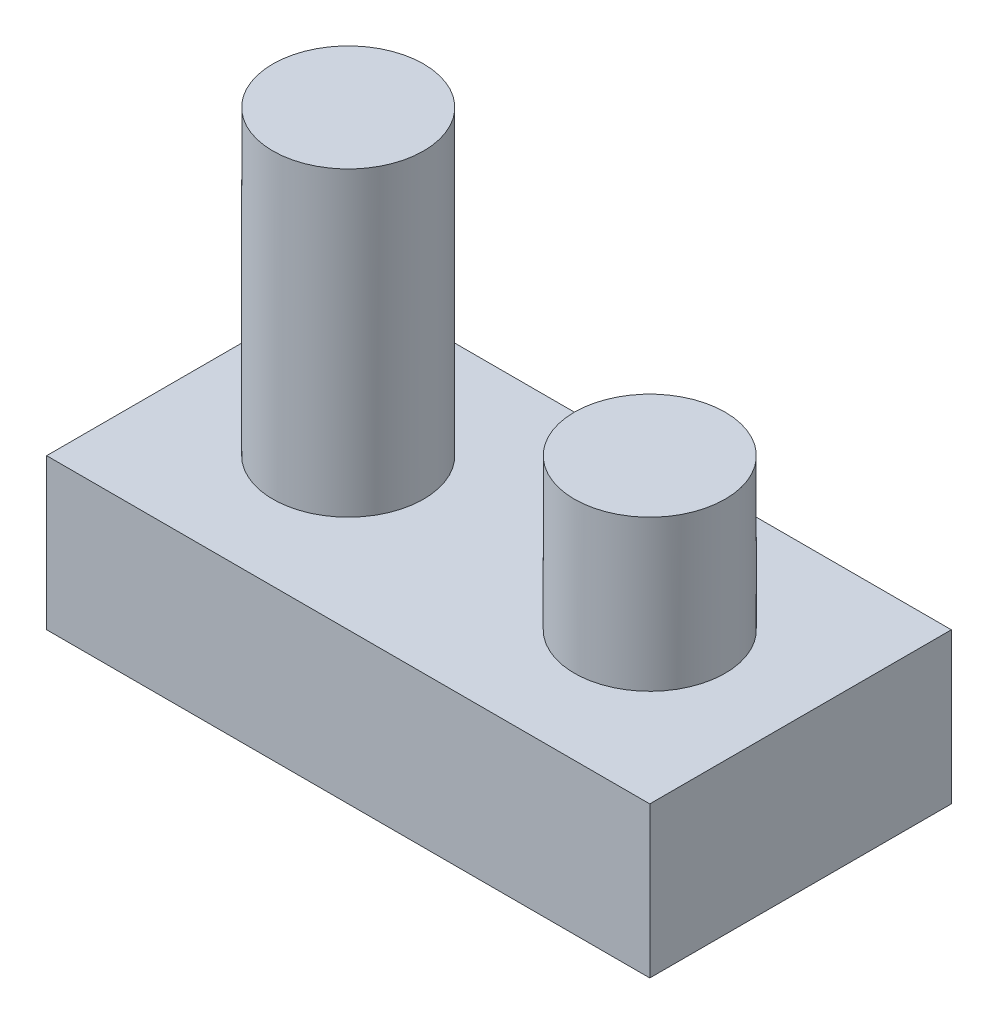
SolidWorks part; units mm, degrees
ref_plane "Front Plane" through (0, 0, 0) normal (0, 0, 1) x (1, 0, 0)
ref_plane "Top Plane" through (0, 0, 0) normal (0, 1, 0) x (1, 0, 0)
ref_plane "Right Plane" through (0, 0, 0) normal (1, 0, 0) x (0, 0, -1)
sketch "Sketch1" plane through (0, 0, 0) normal (0, 1, 0) x (1, 0, 0)
  line L1 (-25.4, -12.7) -> (25.4, -12.7)
  line L2 (-25.4, -12.7) -> (-25.4, 12.7)
  line L3 (-25.4, 12.7) -> (25.4, 12.7)
  line L4 (25.4, -12.7) -> (25.4, 12.7)
  line L5 (-25.4, -12.7) -> (25.4, 12.7) construction
  line L6 (-25.4, 12.7) -> (25.4, -12.7) construction
  point P0 (0, 0)
  dimension "D1" = 50.8
  dimension "D2" = 25.4
extrude "Boss-Extrude1" add sketch "Sketch1" along normal blind 12.7
sketch "Sketch2" plane through (0, 12.7, 0) normal (0, 1, 0) x (1, 0, 0)
  circle A0 centre (-12.7, 0) radius 6.35
  dimension "D1" = 12.7
  dimension "D2" = 12.7
extrude "Boss-Extrude2" add sketch "Sketch2" along normal blind 25.4
sketch "Sketch3" plane through (0, 12.7, 0) normal (0, 1, 0) x (1, 0, 0)
  circle A0 centre (12.7, 0) radius 6.35
  dimension "D1" = 12.7
  dimension "D2" = 12.7
extrude "Boss-Extrude3" add sketch "Sketch3" along normal blind 12.7
